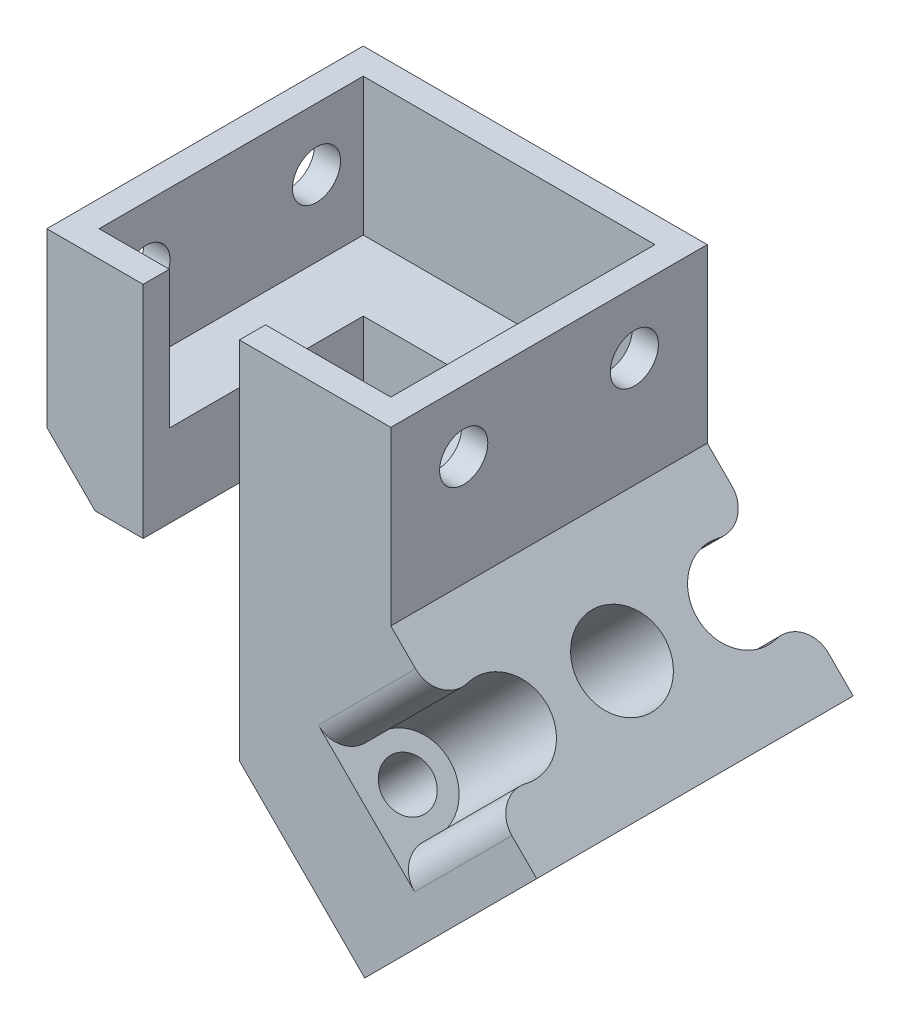
SolidWorks part; units mm, degrees
other "Markup1"
sketch "Sketch10" plane through (35.6066, 12.5, 0) normal (0.0714, 0.5139, 0.8549) x (0.7963, -0.5455, 0.2614)
ref_plane "Front Plane" through (0, 0, 0) normal (0, 0, 1) x (1, 0, 0)
ref_plane "Top Plane" through (0, 0, 0) normal (0, 1, 0) x (1, 0, 0)
ref_plane "Right Plane" through (0, 0, 0) normal (1, 0, 0) x (0, 0, -1)
sketch "Sketch1" plane through (0, 0, 0) normal (0, 1, 0) x (1, 0, 0)
  line L1 (0, 0) -> (25, 0)
  line L2 (0, 0) -> (0, 23)
  line L3 (0, 23) -> (25, 23)
  line L4 (25, 0) -> (25, 23)
  line L5 (0, 0) -> (25, 23) construction
  line L6 (0, 23) -> (25, 0) construction
  point P4 (12.5, 11.5)
  dimension "D1" = 25
  dimension "D2" = 23
extrude "Boss-Extrude1" add sketch "Sketch1" along normal blind 12.5
sketch "Sketch4" plane through (0, 12.5, 0) normal (0, 1, 0) x (1, 0, 0)
  line L0 (25, 0) -> (25, 23) construction
  line L1 (1.9, 21.1) -> (23.1, 21.1)
  line L2 (1.9, 21.1) -> (1.9, 1.9)
  line L3 (1.9, 1.9) -> (23.1, 1.9)
  line L4 (23.1, 21.1) -> (23.1, 1.9)
  line L5 (1.9, 21.1) -> (23.1, 1.9) construction
  line L6 (1.9, 1.9) -> (23.1, 21.1) construction
  line L7 (0, 0) -> (25, 0) construction
  line L8 (0, 23) -> (0, 0) construction
  line L9 (25, 23) -> (0, 23) construction
  point P4 (12.5, 11.5)
  dimension "D1" = 1.9
  dimension "D2" = 1.9
  dimension "D3" = 1.9
  dimension "D4" = 1.9
extrude "Cut-Extrude2" cut sketch "Sketch4" against normal blind 10
sketch "Sketch5" plane through (0, 0, 0) normal (0, 0, 1) x (1, 0, 0)
  line L0 (25, 0) -> (12.5, -12.5)
  line L1 (0.1132, -24.8868) -> (0, 0) construction
  line L2 (0, 0) -> (25, 0)
  line L3 (0, 0) -> (12.5, -12.5)
  line L4 (12.5, -12.5) -> (0.1132, -24.8868) construction
  dimension "D1" = 45
extrude "Boss-Extrude2" add sketch "Sketch5" against normal up to surface (23 mm away) up to face at (12.5, 6.25, -23)
sketch "Sketch2" plane through (0, 12.5, 0) normal (0, 1, 0) x (1, 0, 0)
  line L0 (0, 0) -> (25, 0) construction
  line L1 (7, 0) -> (14, 0)
  line L2 (7, 0) -> (7, 16)
  line L3 (7, 16) -> (14, 16)
  line L4 (14, 0) -> (14, 16)
  line L5 (7, 0) -> (14, 16) construction
  line L6 (7, 16) -> (14, 0) construction
  line L7 (25, 23) -> (0, 23) construction
  line L8 (0, 23) -> (0, 0) construction
  line L9 (0, 23) -> (25, 0) construction
  circle A0 centre (12.5, 11.5) radius 3.5 construction
  point P4 (10.5, 8)
  point P7 (12.5, 23)
  point P16 (12.5, 11.5)
  dimension "D3" = 7
  dimension "D1" = 7
  dimension "D2" = 16
  dimension "D4" = 7
extrude "Cut-Extrude1" cut sketch "Sketch2" against normal blind 16
sketch "Sketch6" plane through (0, 0, 0) normal (0, 0, 1) x (1, 0, 0)
  line L1 (35.6066, -10.6066) -> (25, 0)
  line L2 (35.6066, -10.6066) -> (23.1066, -23.1066)
  line L3 (23.1066, -23.1066) -> (12.5, -12.5)
  line L4 (25, 0) -> (12.5, -12.5)
  line L5 (35.6066, -10.6066) -> (12.5, -12.5) construction
  line L6 (23.1066, -23.1066) -> (25, 0) construction
  point P4 (24.0533, -11.5533)
  dimension "D1" = 15
extrude "Boss-Extrude3" add sketch "Sketch6" against normal up to surface (23 mm away) up to face at (12.5, 2.5, -23)
sketch "Sketch7" plane through (12.5, 12.5, 0) normal (0.7071, 0.7071, 0) x (0, 0, -1)
  line L0 (23, -25.1777) -> (0, -25.1777) construction
  line L1 (23, -17.6777) -> (23, -32.6777) construction
  line L2 (0, -32.6777) -> (0, -17.6777) construction
  circle A0 centre (20, -25.1777) radius 1.75
  circle A1 centre (3, -25.1777) radius 1.75
  circle A2 centre (11.5, -25.1777) radius 1.75
  dimension "D1" = 3.5
  dimension "D2" = 3
  dimension "D3" = 3
extrude "Cut-Extrude3" cut sketch "Sketch7" against normal through all
sketch "Sketch8" plane through (12.5, 12.5, 0) normal (0.7071, 0.7071, 0) x (0, 0, -1)
  circle A0 centre (20, -25.1777) radius 3.05
  circle A1 centre (11.5, -25.1777) radius 3.05
  circle A2 centre (3, -25.1777) radius 3.05
  dimension "D2" = 6.1
extrude "Cut-Extrude8" cut sketch "Sketch8" against normal blind 10
fillet "Fillet1" radius 2 4 edges at (26.3789, -8.4499, 0) (27.1567, -9.2277, 0) (27.1567, -9.2277, -23) (26.3789, -8.4499, -23)
sketch "Sketch9" plane through (0, 0, 0) normal (0, 0, 1) x (1, 0, 0)
  line L1 (0, 0) -> (23.1066, -23.1066) construction
  line L2 (7, -7) -> (14, -14)
  line L3 (14, -14) -> (14, -3.5)
  line L4 (14, -3.5) -> (7, -3.5)
  line L5 (7, -3.5) -> (3.5, -3.5)
  line L6 (3.5, -3.5) -> (7, -7)
extrude "Cut-Extrude9" cut sketch "Sketch9" against normal blind 2
sketch "Sketch11" plane through (25, 0, 0) normal (1, 0, 0) x (0, 0, -1)
  line L0 (0, 8) -> (5.3, 8) construction
  line L1 (0, 12.5) -> (0, 0) construction
  line L2 (5.3, 8) -> (11.5, 0) construction
  line L3 (0, 0) -> (23, 0) construction
  line L4 (11.5, 0) -> (11.5, 12.5) construction
  line L5 (0, 12.5) -> (23, 12.5) construction
  circle A0 centre (5.3, 8) radius 1.75
  circle A1 centre (17.7, 8) radius 1.75
  dimension "D1" = 3.5
  dimension "D2" = 5.3
  dimension "D3" = 8
extrude "Cut-Extrude10" cut sketch "Sketch11" against normal through all
sketch "Sketch12" plane through (0, 0, -2) normal (0, 0, 1) x (1, 0, 0)
  line L0 (3.5, -3.5) -> (14, -3.5)
  line L1 (14, -3.5) -> (14, -14)
  line L2 (14, -14) -> (3.5, -3.5)
extrude "Cut-Extrude11" cut sketch "Sketch12" against normal up to surface (14 mm away) up to face at (10.5, -0.5, -16)
